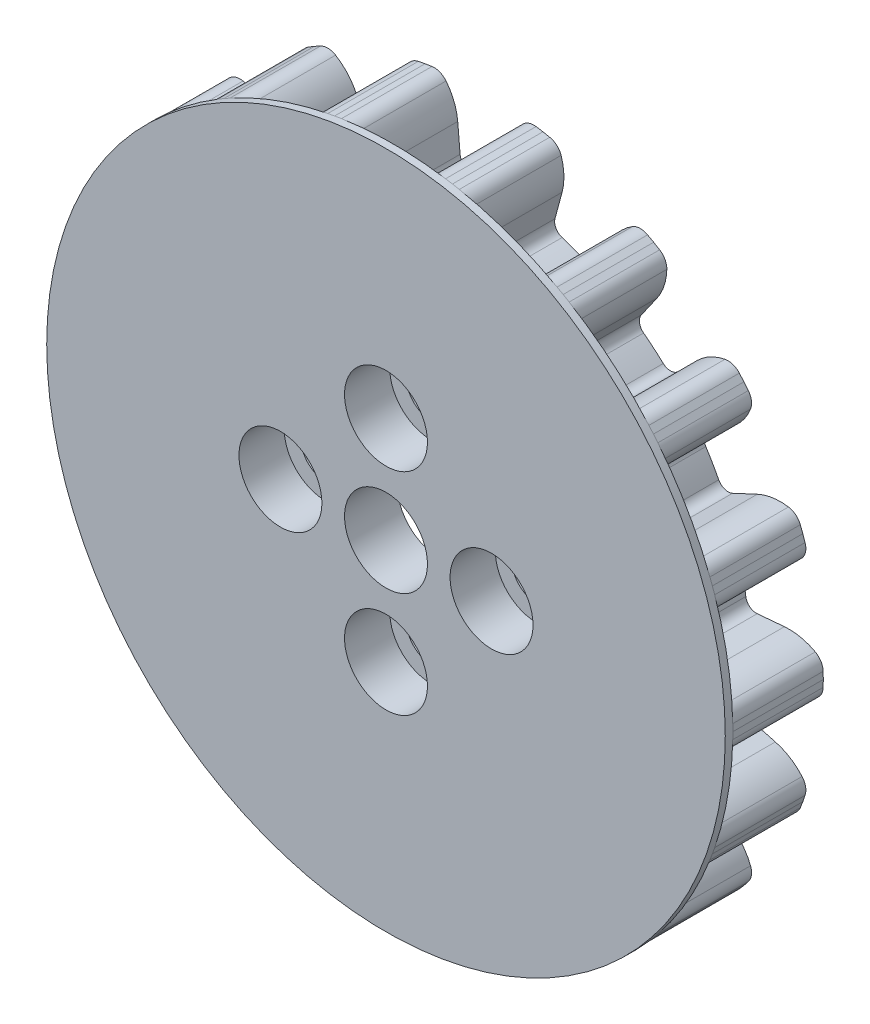
SolidWorks part; units mm, degrees
ref_plane "Plan de face" through (0, 0, 0) normal (0, 0, 1) x (1, 0, 0)
ref_plane "Plan de dessus" through (0, 0, 0) normal (0, 1, 0) x (1, 0, 0)
ref_plane "Plan de droite" through (0, 0, 0) normal (1, 0, 0) x (0, 0, -1)
sketch "Esquisse4" plane through (0, 0, 0) normal (0, 0, 1) x (1, 0, 0)
  line L0 (0, 0) -> (15.5601, 0) construction
  line L1 (0, 0) -> (17.2426, 1.5085) construction
  line L2 (0, 0) -> (17.0187, 3.0009) construction
  line L3 (0, 0) -> (17.2619, 0.7537) construction
  line L4 (17.4334, 1.5252) -> (19.9239, 1.7431)
  line L5 (17.2341, 3.0388) -> (0, 0)
  line L6 (22.4786, 0.9814) -> (22.5, 0)
  line L7 (22.4786, -0.9814) -> (22.5, 0)
  line L8 (17.4334, -1.5252) -> (19.9239, -1.7431)
  line L9 (17.2341, -3.0388) -> (0, 0)
  circle A0 centre (0, 0) radius 17.5 construction
  circle A1 centre (0, 0) radius 20 construction
  circle A2 centre (0, 0) radius 22.5 construction
  arc A3 (22.4786, 0.9814) -> (19.9239, 1.7431) centre (20.2394, -1.8636) ccw
  arc A4 (17.4334, 1.5252) -> (17.2341, 3.0388) centre (0, 0) ccw
  arc A5 (22.4786, -0.9814) -> (19.9239, -1.7431) centre (20.2394, 1.8636) cw
  arc A6 (17.4334, -1.5252) -> (17.2341, -3.0388) centre (0, 0) cw
  dimension "D1" = 45
  dimension "D2" = 40
  dimension "D3" = 35
  dimension "D4" = 10
  dimension "D5" = 5
  dimension "D6" = 2.5
extrude "Boss.-Extru.4" add sketch "Esquisse4" along normal blind 6 contours A6 L8 A5 L7 L6 A3 L4 A4 L5 L9
fillet "Congé1" radius 0.7 2 edges at (17.4334, 1.5252, 3) (17.4334, -1.5252, 3)
fillet "Congé2" radius 1 2 edges at (22.4786, 0.9814, 3) (22.4786, -0.9814, 3)
pattern_circular "Répétition circulaire1" count 18 over 360 about axis through (0, 0, 0) along (0, 0, 1) of bodies 103
sketch "Esquisse8" plane through (0, 0, 6) normal (0, 0, 1) x (1, 0, 0)
  circle A0 centre (0, 0) radius 22.5
extrude "Boss.-Extru.5" add sketch "Esquisse8" along normal blind 0.5
sketch "Esquisse9" plane through (0, 0, 0) normal (0, 0, -1) x (-1, 0, 0)
  circle A0 centre (0, 0) radius 10.5
  dimension "D1" = 21
extrude "Enlèv. mat.-Extru.1" cut sketch "Esquisse9" against normal blind 3
sketch "Esquisse10" plane through (0, 0, 3) normal (0, 0, -1) x (-1, 0, 0)
  line L0 (0, 7) -> (0, 0) construction
  circle A0 centre (0, 0) radius 2.75
  circle A1 centre (0, 7) radius 1.65
  circle A2 centre (7, 0) radius 1.65
  circle A3 centre (0, -7) radius 1.65
  circle A4 centre (-7, 0) radius 1.65
  point P14 (0, 0)
  dimension "D1" = 5.5
  dimension "D2" = 3.3
  dimension "D3" = 7
  dimension "D4" = 4
extrude "Enlèv. mat.-Extru.2" cut sketch "Esquisse10" against normal up to next
sketch "Esquisse11" plane through (0, 0, 6.5) normal (0, 0, 1) x (1, 0, 0)
  circle A0 centre (0, 7) radius 2.75
  circle A1 centre (7, 0) radius 2.75
  circle A2 centre (0, -7) radius 2.75
  circle A3 centre (-7, 0) radius 2.75
  point P12 (0, 0)
  dimension "D1" = 5.5
  dimension "D2" = 4
extrude "Enlèv. mat.-Extru.3" cut sketch "Esquisse11" against normal blind 3
